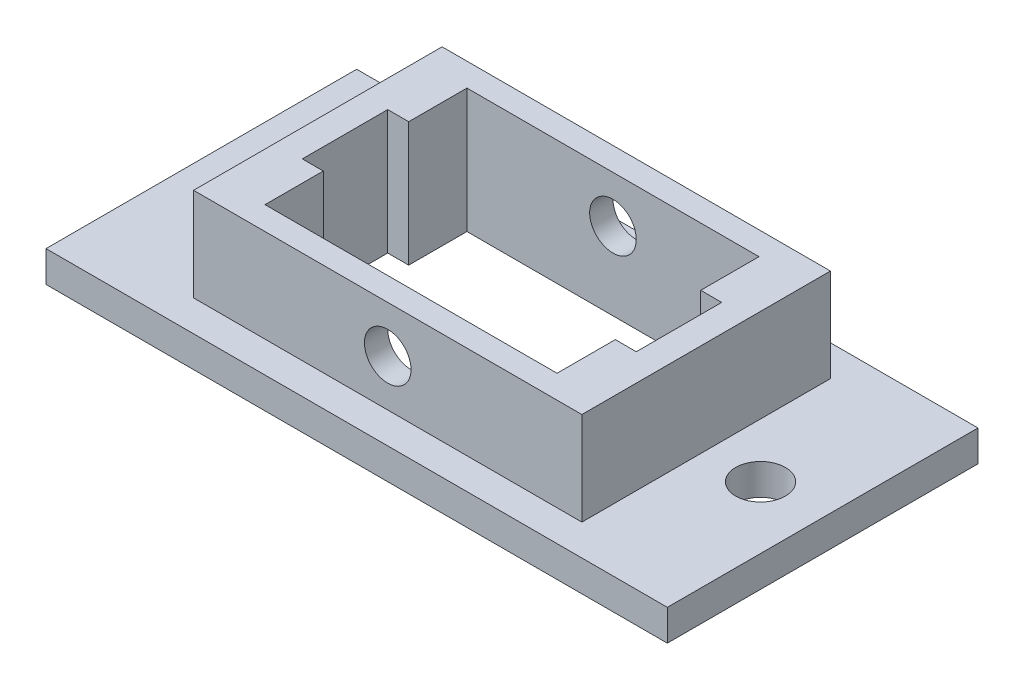
SolidWorks part; units mm, degrees
ref_plane "Front Plane" through (0, 0, 0) normal (0, 0, 1) x (1, 0, 0)
ref_plane "Top Plane" through (0, 0, 0) normal (0, 1, 0) x (1, 0, 0)
ref_plane "Right Plane" through (0, 0, 0) normal (1, 0, 0) x (0, 0, -1)
sketch "Sketch1" plane through (0, 0, 0) normal (0, 1, 0) x (1, 0, 0)
  line L0 (-17.6364, -3.4545) -> (22.3636, -3.4545) construction
  line L1 (-17.6364, 6.5455) -> (22.3636, 6.5455) construction
  line L2 (-17.6364, 6.5455) -> (-17.6364, -13.4545) construction
  line L3 (-17.6364, -13.4545) -> (22.3636, -13.4545) construction
  line L4 (22.3636, 6.5455) -> (22.3636, -13.4545) construction
  line L5 (-7.0364, 3.0455) -> (11.7636, 3.0455)
  line L6 (-7.0364, 3.0455) -> (-7.0364, -0.7045)
  line L7 (-7.0364, -9.9545) -> (11.7636, -9.9545)
  line L8 (11.7636, 3.0455) -> (11.7636, -0.7045)
  line L9 (2.3636, 6.5455) -> (2.3636, -13.4545) construction
  line L10 (-7.0364, -6.2045) -> (-7.0364, -9.9545)
  line L11 (-8.3864, -0.7045) -> (-7.0364, -0.7045)
  line L12 (-8.3864, -0.7045) -> (-8.3864, -6.2045)
  line L13 (-8.3864, -6.2045) -> (-7.0364, -6.2045)
  line L14 (13.1136, -0.7045) -> (13.1136, -6.2045)
  line L15 (11.7636, -6.2045) -> (11.7636, -9.9545)
  line L16 (11.7636, -0.7045) -> (13.1136, -0.7045)
  line L17 (11.7636, -6.2045) -> (13.1136, -6.2045)
  point P13 (2.3636, 3.0455)
  point P18 (18.647, -7.8159)
  point P20 (-8.3864, -3.4545)
  dimension "D1" = 20
  dimension "D2" = 40
  dimension "D3" = 13
  dimension "D4" = 18.8
  dimension "D5" = 21.5
  dimension "D6" = 5.5
  dimension "D7" = 6.5
  dimension "D8" = 10.75
sketch "Sketch2" plane through (0, 0, 0) normal (0, 1, 0) x (1, 0, 0)
  line L1 (-17.6364, -13.4545) -> (22.3636, -13.4545)
  line L2 (-17.6364, -13.4545) -> (-17.6364, 6.5455)
  line L3 (-17.6364, 6.5455) -> (22.3636, 6.5455)
  line L4 (22.3636, -13.4545) -> (22.3636, 6.5455)
extrude "Boss-Extrude1" add sketch "Sketch2" along normal blind 2
sketch "Sketch3" plane through (0, 0, 0) normal (0, -1, 0) x (1, 0, 0)
  line L0 (-17.6364, 3.4545) -> (22.3636, 3.4545) construction
  line L1 (-10.1364, 11.4545) -> (14.8636, 11.4545)
  line L2 (-10.1364, 11.4545) -> (-10.1364, -4.5455)
  line L3 (-10.1364, -4.5455) -> (14.8636, -4.5455)
  line L4 (14.8636, 11.4545) -> (14.8636, -4.5455)
  line L5 (2.3636, -6.5455) -> (2.3636, 13.4545) construction
  point P4 (-10.1364, 3.4545)
  point P7 (2.3636, 11.4545)
  dimension "D1" = 25
  dimension "D2" = 16
extrude "Boss-Extrude2" add sketch "Sketch3" against normal blind 8
extrude "Cut-Extrude1" cut sketch "Sketch1" along normal blind 10
sketch "Sketch5" plane through (0, 0, 0) normal (0, -1, 0) x (1, 0, 0)
  line L0 (-17.6364, 3.4545) -> (22.3636, 3.4545) construction
  line L1 (18.3636, 3.4545) -> (-13.6364, 3.4545) construction
  line L2 (2.3636, -6.5455) -> (2.3636, 13.4545) construction
  circle A0 centre (18.3636, 3.4545) radius 1.6
  circle A1 centre (-13.6364, 3.4545) radius 1.6
  point P2 (2.3636, 3.4545)
  dimension "D1" = 3.2
  dimension "D2" = 32
extrude "Cut-Extrude2" cut sketch "Sketch5" against normal blind 10
sketch "Sketch6" plane through (0, 0, 11.4545) normal (0, 0, 1) x (1, 0, 0)
  line L0 (-10.1364, 8) -> (-10.1364, 2) construction
  line L1 (-10.1364, 5) -> (14.8636, 5) construction
  line L2 (14.8636, 8) -> (14.8636, 2) construction
  circle A0 centre (2.3636, 5) radius 1.5
  point P2 (0, 0)
  point P9 (2.3636, 5)
  dimension "D1" = 3
extrude "Cut-Extrude3" cut sketch "Sketch6" against normal blind 30
